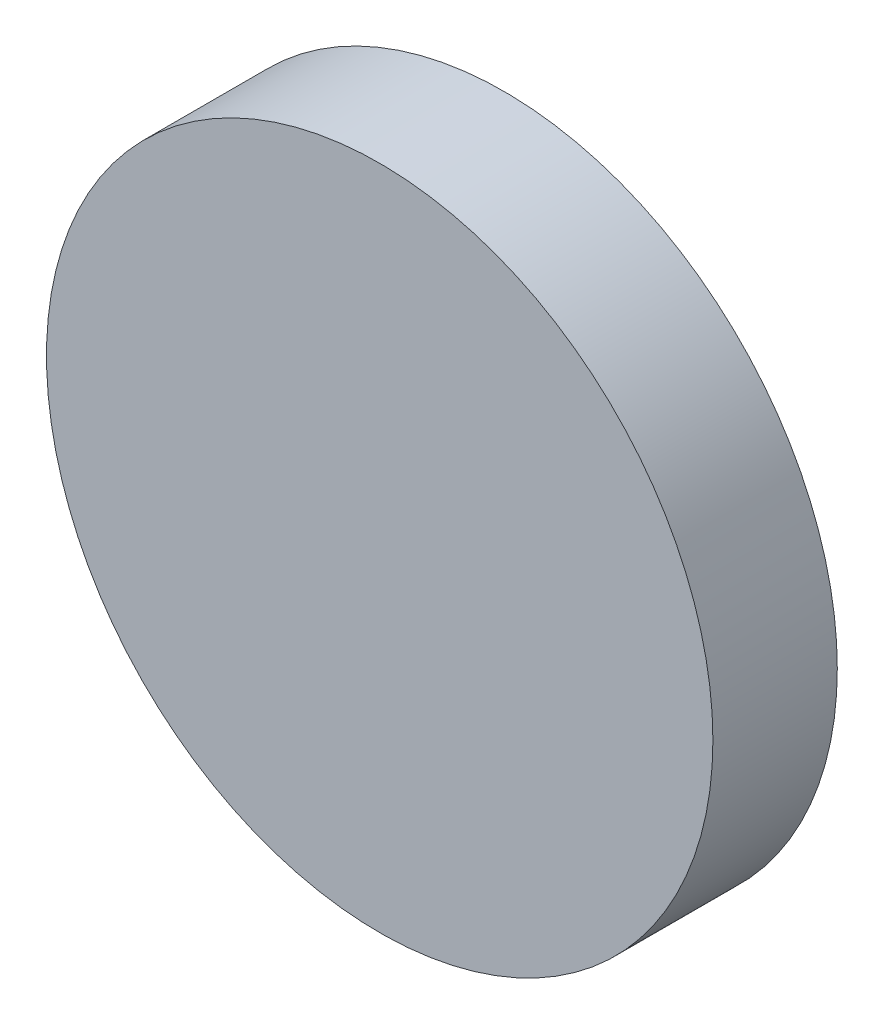
SolidWorks part; units mm, degrees
ref_plane "Alzado" through (0, 0, 0) normal (0, 0, 1) x (1, 0, 0)
ref_plane "Planta" through (0, 0, 0) normal (0, 1, 0) x (1, 0, 0)
ref_plane "Vista lateral" through (0, 0, 0) normal (1, 0, 0) x (0, 0, -1)
sketch "Model" plane through (0, 0, 0) normal (0, 0, 1) x (1, 0, 0)
  circle A0 centre (50, 32.0274) radius 8.0351
extrude "Saliente-Extruir1" add sketch "Model" along normal blind 3
